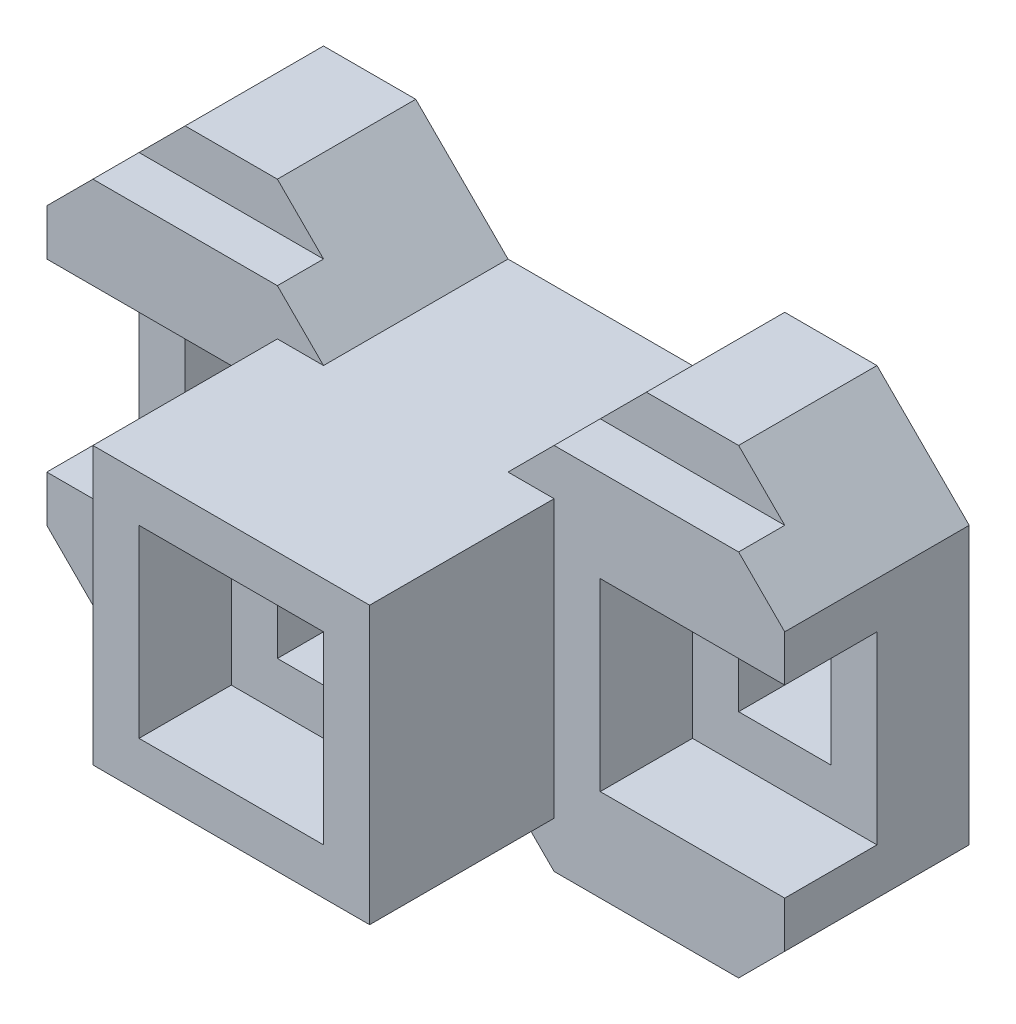
SolidWorks part; units mm, degrees
ref_plane "Front Plane" through (0, 0, 0) normal (0, 0, 1) x (1, 0, 0)
ref_plane "Top Plane" through (0, 0, 0) normal (0, 1, 0) x (1, 0, 0)
ref_plane "Right Plane" through (0, 0, 0) normal (1, 0, 0) x (0, 0, -1)
sketch "Sketch1" plane through (0, 0, 0) normal (0, 0, 1) x (1, 0, 0)
  line L1 (0, 0) -> (60, 0)
  line L2 (0, 0) -> (0, 60)
  line L3 (0, 60) -> (60, 60)
  line L4 (60, 0) -> (60, 60)
  dimension "D1" = 60
  dimension "D2" = 60
extrude "Boss-Extrude1" add sketch "Sketch1" along normal blind 80
sketch "Sketch2" plane through (0, 0, 80) normal (0, 0, 1) x (1, 0, 0)
  line L1 (50, 50) -> (10, 50)
  line L2 (50, 50) -> (50, 10)
  line L3 (50, 10) -> (10, 10)
  line L4 (10, 50) -> (10, 10)
  dimension "D1" = 40
  dimension "D2" = 40
  dimension "D3" = 10
  dimension "D4" = 10
extrude "Cut-Extrude1" cut sketch "Sketch2" against normal blind 20
sketch "Sketch3" plane through (0, 0, 60) normal (0, 0, 1) x (1, 0, 0)
  line L1 (20, 40) -> (40, 40)
  line L2 (20, 40) -> (20, 20)
  line L3 (20, 20) -> (40, 20)
  line L4 (40, 40) -> (40, 20)
  dimension "D1" = 20
  dimension "D2" = 20
  dimension "D3" = 10
  dimension "D4" = 10
extrude "Cut-Extrude2" cut sketch "Sketch3" against normal blind 136
sketch "Sketch5" plane through (0, 0, 0) normal (0, 0, -1) x (-1, 0, 0)
  line L0 (-10, 60) -> (10, 80)
  line L1 (-60, 60) -> (0, 60) construction
  line L2 (10, 80) -> (30, 80)
  line L3 (30, 80) -> (50, 60)
  line L4 (50, 60) -> (50, 0)
  line L5 (50, 0) -> (30, -20)
  line L6 (30, -20) -> (10, -20)
  line L7 (10, -20) -> (-10, 0)
  line L8 (0, 0) -> (-60, 0) construction
  line L9 (-10, 60) -> (0, 60)
  line L10 (0, 60) -> (0, 0)
  line L11 (0, 0) -> (-10, 0)
  line L13 (0, 0) -> (0, 60)
  line L14 (0, 60) -> (-60, 60)
  line L15 (-60, 60) -> (-60, 0)
  line L16 (-60, 0) -> (0, 0)
  line L18 (-10, 60) -> (-60, 60)
  line L19 (-60, 60) -> (-60, 0)
  line L20 (-60, 0) -> (-10, 0)
  line M9 (0, 0) -> (0, 60)
  line M10 (0, 60) -> (-60, 60)
  line M12 (-60, 0) -> (0, 0)
  dimension "D1" = 20
  dimension "D2" = 20
  dimension "D3" = 20
  dimension "D4" = 20
  dimension "D5" = 10
  dimension "D6" = 20
  dimension "D7" = 10
  dimension "D8" = 20
  dimension "D9" = 20
  dimension "D10" = 0
extrude "Boss-Extrude2" add sketch "Sketch5" against normal blind 40 contours L7 L6 L5 L4 L3 L2 L0 M10 M9 M12
sketch "Sketch6" plane through (0, 0, 40) normal (0, 0, 1) x (1, 0, 0)
  line L0 (0, 70) -> (-40, 70)
  line L1 (10, 60) -> (-10, 80) construction
  line L2 (-30, 80) -> (-50, 60) construction
  line L3 (-40, 70) -> (-30, 80)
  line L4 (-30, 80) -> (-10, 80)
  line L5 (-10, 80) -> (0, 70)
  line L6 (-40, -10) -> (0, -10)
  line L7 (-50, 0) -> (-30, -20) construction
  line L8 (-10, -20) -> (10, 0) construction
  line L9 (-40, 70) -> (-30, 80)
  line L10 (-30, 80) -> (-10, 80)
  line L11 (-10, 80) -> (0, 70)
  line L12 (0, -10) -> (-10, -20)
  line L13 (-10, -20) -> (-30, -20)
  line L14 (-30, -20) -> (-40, -10)
  line M1 (-10, -20) -> (10, 0)
  line M5 (10, 60) -> (-10, 80)
  line M6 (-10, 80) -> (-30, 80)
  line M7 (-30, 80) -> (-50, 60)
  line M9 (-50, 0) -> (-30, -20)
  line M10 (-30, -20) -> (-10, -20)
  dimension "D1" = 10
  dimension "D2" = 10
extrude "Cut-Extrude3" cut sketch "Sketch6" against normal blind 10 contours L0 M5 M6 M7 | L6 M9 M10 M1
sketch "Sketch7" plane through (0, 0, 40) normal (0, 0, 1) x (1, 0, 0)
  line L0 (-50, 60) -> (-50, 0) construction
  line L1 (-50, 50) -> (-10, 50)
  line L2 (-50, 50) -> (-50, 10)
  line L3 (-50, 10) -> (-10, 10)
  line L4 (-10, 50) -> (-10, 10)
  dimension "D1" = 40
  dimension "D2" = 40
  dimension "D3" = 10
extrude "Cut-Extrude4" cut sketch "Sketch7" against normal blind 20
sketch "Sketch8" plane through (0, 0, 20) normal (0, 0, 1) x (1, 0, 0)
  line L1 (-40, 40) -> (-20, 40)
  line L2 (-40, 40) -> (-40, 20)
  line L3 (-40, 20) -> (-20, 20)
  line L4 (-20, 40) -> (-20, 20)
  dimension "D1" = 20
  dimension "D2" = 20
  dimension "D3" = 10
  dimension "D4" = 10
extrude "Cut-Extrude5" cut sketch "Sketch8" against normal blind 20
sketch "Sketch9" plane through (0, 0, 0) normal (0, 0, -1) x (-1, 0, 0)
  line L0 (-50, 60) -> (-70, 80)
  line L1 (-60, 60) -> (-10, 60) construction
  line L2 (-70, 80) -> (-90, 80)
  line L3 (-90, 80) -> (-110, 60)
  line L4 (-110, 60) -> (-110, 0)
  line L5 (-110, 0) -> (-90, -20)
  line L6 (-90, -20) -> (-70, -20)
  line L7 (-70, -20) -> (-50, 0)
  line L9 (-50, 60) -> (-60, 60)
  line L10 (-60, 60) -> (-60, 0)
  line L11 (-60, 0) -> (-50, 0)
  dimension "D1" = 20
  dimension "D2" = 20
  dimension "D3" = 10
  dimension "D4" = 20
  dimension "D5" = 20
  dimension "D6" = 20
  dimension "D7" = 20
  dimension "D8" = 20
  dimension "D9" = 20
  dimension "D10" = 20
  dimension "D11" = 0
extrude "Boss-Extrude3" add sketch "Sketch9" against normal blind 40
sketch "Sketch10" plane through (0, 0, 40) normal (0, 0, 1) x (1, 0, 0)
  line L0 (60, 70) -> (100, 70)
  line L1 (50, 60) -> (70, 80) construction
  line L2 (90, 80) -> (110, 60) construction
  line L3 (60, -10) -> (100, -10)
  line L4 (70, -20) -> (50, 0) construction
  line L5 (110, 0) -> (90, -20) construction
  line L6 (60, 70) -> (70, 80)
  line L7 (70, 80) -> (90, 80)
  line L8 (90, 80) -> (100, 70)
  line L9 (60, -10) -> (70, -20)
  line L10 (70, -20) -> (90, -20)
  line L11 (90, -20) -> (100, -10)
extrude "Cut-Extrude6" cut sketch "Sketch10" against normal blind 10
sketch "Sketch11" plane through (0, 0, 40) normal (0, 0, 1) x (1, 0, 0)
  line L0 (110, 60) -> (110, 0) construction
  line L1 (110, 50) -> (70, 50)
  line L2 (110, 50) -> (110, 10)
  line L3 (110, 10) -> (70, 10)
  line L4 (70, 50) -> (70, 10)
  dimension "D1" = 40
  dimension "D2" = 40
  dimension "D3" = 10
extrude "Cut-Extrude7" cut sketch "Sketch11" against normal blind 20
sketch "Sketch12" plane through (0, 0, 20) normal (0, 0, 1) x (1, 0, 0)
  line L1 (100, 40) -> (80, 40)
  line L2 (100, 40) -> (100, 20)
  line L3 (100, 20) -> (80, 20)
  line L4 (80, 40) -> (80, 20)
  dimension "D1" = 20
  dimension "D2" = 20
  dimension "D3" = 10
  dimension "D4" = 10
extrude "Cut-Extrude8" cut sketch "Sketch12" against normal blind 20
